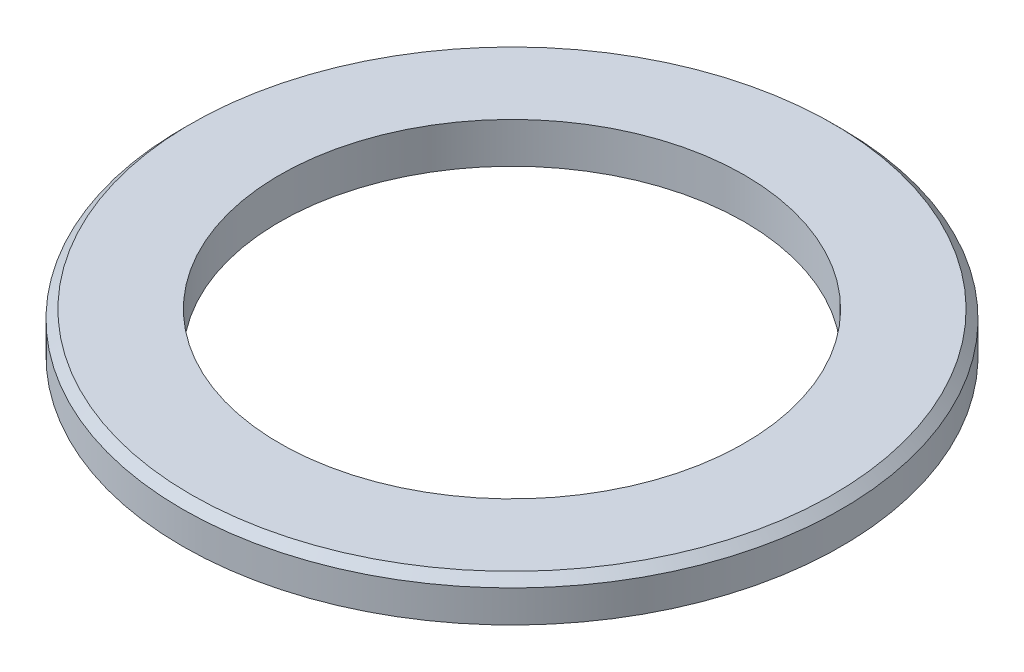
SolidWorks part; units mm, degrees
ref_plane "Front Plane" through (0, 0, 0) normal (0, 0, 1) x (1, 0, 0)
ref_plane "Top Plane" through (0, 0, 0) normal (0, 1, 0) x (1, 0, 0)
ref_plane "Right Plane" through (0, 0, 0) normal (1, 0, 0) x (0, 0, -1)
sketch "Sketch1" plane through (0, 0, 0) normal (0, 0, 1) x (1, 0, 0)
  line L0 (0, 0) -> (0, 21.8192) construction
  line L1 (27.5, 0) -> (29.9364, 0)
  line L2 (39, 0) -> (39, 4.8)
  line L3 (39, 4.8) -> (27.5, 4.8)
  line L4 (27.5, 4.8) -> (27.5, 0)
  line L5 (29.9364, 0) -> (34.3995, 0) construction
  line L6 (34.3995, 0) -> (39, 0)
  arc A0 (29.9364, 0) -> (34.3995, 0) centre (32.168, -3.3197) cw
  dimension "D4" = 4
  dimension "D1" = 78
  dimension "D2" = 55
  dimension "D3" = 4.8
revolve "Revolve1" add sketch "Sketch1" angle 360 about L0
chamfer "Chamfer1" distance 1 angle 45 1 edges at (0, 4.8, -39)
